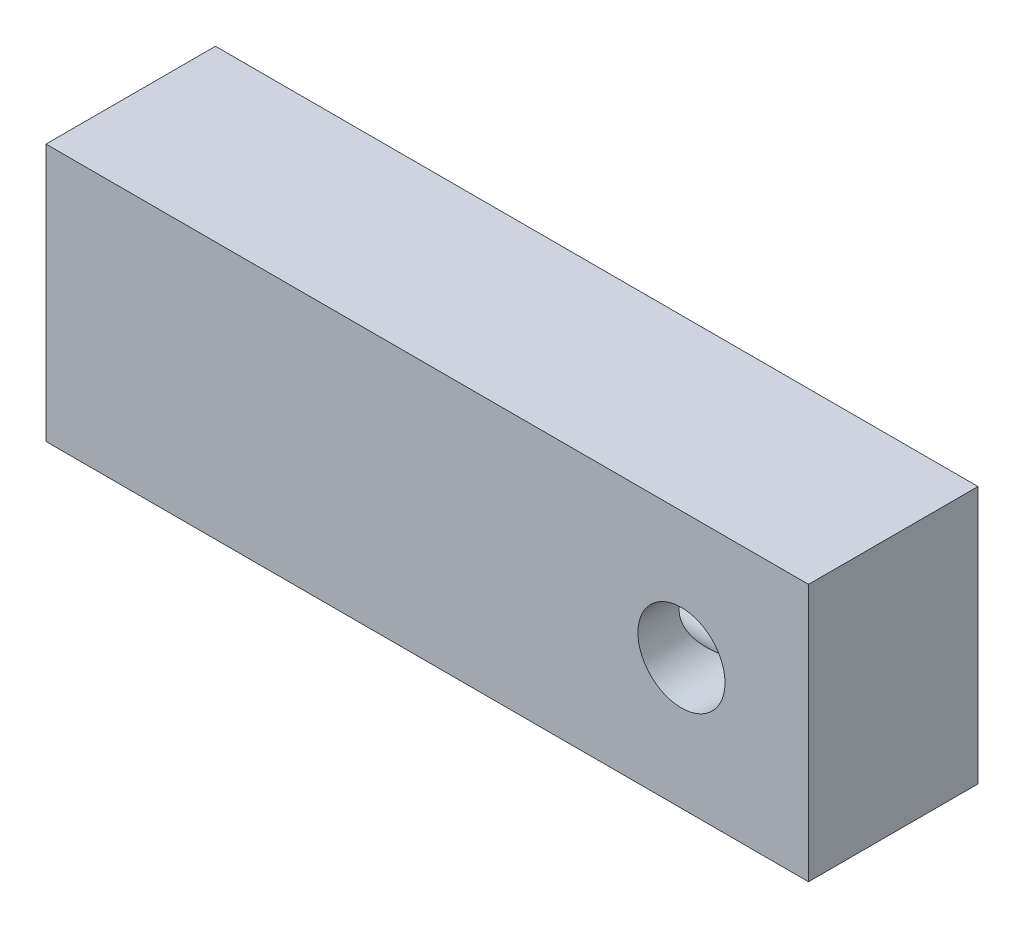
SolidWorks part; units mm, degrees
material "6061-T6 (SS)"
ref_plane "Front Plane" through (0, 0, 0) normal (0, 0, 1) x (1, 0, 0)
ref_plane "Top Plane" through (0, 0, 0) normal (0, 1, 0) x (1, 0, 0)
ref_plane "Right Plane" through (0, 0, 0) normal (1, 0, 0) x (0, 0, -1)
sketch "Sketch1" plane through (0, 0, 0) normal (0, 0, 1) x (1, 0, 0)
  line L1 (-14.2875, -4.826) -> (14.2875, -4.826)
  line L2 (-14.2875, -4.826) -> (-14.2875, 4.826)
  line L3 (-14.2875, 4.826) -> (14.2875, 4.826)
  line L4 (14.2875, -4.826) -> (14.2875, 4.826)
  line L5 (-14.2875, -4.826) -> (14.2875, 4.826) construction
  line L6 (-14.2875, 4.826) -> (14.2875, -4.826) construction
  point P1 (0, 0)
  dimension "D1" = 28.575
  dimension "D2" = 9.652
extrude "Boss-Extrude1" add sketch "Sketch1" along normal blind 6.35
hole_wizard "#4 Clearance Hole1" positions "Sketch3" profile "Sketch2" hole size "#4" standard "ANSI Inch" end condition through all
sketch "Sketch3" plane through (0, 0, 6.35) normal (0, 0, 1) x (1, 0, 0)
  line L0 (14.2875, -4.826) -> (14.2875, 4.826) construction
  line L1 (14.2875, 4.826) -> (-14.2875, 4.826) construction
  point P0 (9.525, 0.0635)
  dimension "D1" = 4.7625
  dimension "D2" = 4.7625
sketch "Sketch2" plane through (9.525, 0.0635, 6.35) normal (1, 0, 0) x (0, -1, 0)
  line L0 (0, 0) -> (0, 6.35)
  line L1 (0, 6.35) -> (1.6319, 6.35)
  line L2 (1.6319, 6.35) -> (1.6319, 0)
  line L5 (1.6319, 0) -> (0, 0)
  line L11 (0, -6.35) -> (0, 107.95) construction
  dimension "Thru Hole Dia." = 3.2639
  dimension "Thru Hole Depth" = 6.35
hole_wizard "#4 Clearance Hole2" positions "Sketch5" profile "Sketch6" hole size "#4" standard "ANSI Inch"
sketch "Sketch5" plane through (-14.2875, 0, 0) normal (-1, 0, 0) x (0, 0, 1)
  line L0 (6.35, 4.826) -> (6.35, -4.826) construction
  point P0 (3.175, 0)
  point P3 (6.35, 0)
  dimension "D1" = 3.175
sketch "Sketch6" plane through (-14.2875, 0, 3.175) normal (0, 1, 0) x (0, 0, 1)
  line L0 (0, 0) -> (0, 24.7921)
  line L1 (0, 24.7921) -> (1.6319, 23.8115)
  line L2 (1.6319, 23.8115) -> (1.6319, 0)
  line L5 (1.6319, 0) -> (0, 0)
  line L10 (0, 24.7921) -> (-1.632, 23.8115) construction
  line L11 (0, -6.35) -> (0, 107.95) construction
  dimension "Hole Dia." = 3.2639
  dimension "Hole Depth" = 23.8115
  dimension "Drill Angle" = 118
